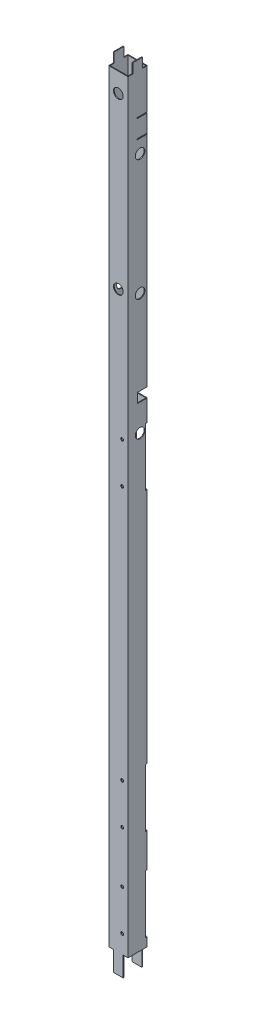
SolidWorks part; units mm, degrees
ref_plane "Front Plane" through (0, 0, 0) normal (0, 0, 1) x (1, 0, 0)
ref_plane "Top Plane" through (0, 0, 0) normal (0, 1, 0) x (1, 0, 0)
ref_plane "Right Plane" through (0, 0, 0) normal (1, 0, 0) x (0, 0, -1)
sketch "Sketch1" plane through (0, 0, 0) normal (0, 1, 0) x (1, 0, 0)
  line L0 (1.5, 1.5) -> (38.5, 1.5)
  line L1 (0.5, 0) -> (39.5, 0)
  line L2 (0, 0.5) -> (0, 39.5)
  line L3 (0.5, 40) -> (39.5, 40)
  line L4 (40, 0.5) -> (40, 39.5)
  line L5 (38.5, 1.5) -> (38.5, 38.5)
  line L6 (1.5, 38.5) -> (38.5, 38.5)
  line L7 (1.5, 1.5) -> (1.5, 38.5)
  arc A0 (39.5, 0) -> (40, 0.5) centre (39.5, 0.5) ccw
  arc A1 (0.5, 0) -> (0, 0.5) centre (0.5, 0.5) cw
  arc A2 (0, 39.5) -> (0.5, 40) centre (0.5, 39.5) cw
  arc A3 (39.5, 40) -> (40, 39.5) centre (39.5, 39.5) cw
  arc A4 (38.5, 1.5) -> (38.5, 1.5) centre (38.5, 1.5) ccw
  arc A5 (38.5, 38.5) -> (38.5, 38.5) centre (38.5, 38.5) cw
  arc A6 (1.5, 38.5) -> (1.5, 38.5) centre (1.5, 38.5) cw
  arc A7 (1.5, 1.5) -> (1.5, 1.5) centre (1.5, 1.5) cw
  point P9 (0, 0)
  dimension "D3" = 0.5
  dimension "D1" = 40
  dimension "D2" = 40
  dimension "D4" = 1.5
extrude "Boss-Extrude1" add sketch "Sketch1" along normal blind 1637.5
sketch "Sketch2" plane through (40, 0, 0) normal (1, 0, 0) x (0, 0, -1)
  line L0 (20, 1637.5) -> (20, 1563.8814) construction
  line L1 (40, 1637.5) -> (30, 1637.5)
  line L2 (40, 1637.5) -> (40, 1617.5)
  line L3 (40, 1617.5) -> (30, 1617.5)
  line L4 (30, 1637.5) -> (30, 1617.5)
  line L5 (0.5, 1637.5) -> (39.5, 1637.5) construction
  line L6 (10, 1637.5) -> (10, 1617.5)
  line L7 (0, 1617.5) -> (10, 1617.5)
  line L8 (0, 1637.5) -> (0, 1617.5)
  line L9 (0, 1637.5) -> (10, 1637.5)
  dimension "D1" = 20
  dimension "D2" = 10
extrude "Cut-Extrude1" cut sketch "Sketch2" against normal blind 40
sketch "Sketch3" plane through (40, 0, 0) normal (1, 0, 0) x (0, 0, -1)
  line L0 (40, 1617.5) -> (40, 0) construction
  line L1 (40, 1535) -> (19, 1535)
  line L2 (40, 1535) -> (40, 1533)
  line L3 (40, 1533) -> (19, 1533)
  line L4 (19, 1535) -> (19, 1533)
  line L5 (30, 1617.5) -> (39.5, 1617.5) construction
  line L6 (40, 1515) -> (25.1946, 1515) construction
  line L7 (40, 1617.5) -> (40, 0) construction
  line L8 (19, 1495) -> (19, 1497)
  line L9 (40, 1497) -> (19, 1497)
  line L10 (40, 1495) -> (40, 1497)
  line L11 (40, 1495) -> (19, 1495)
  point P9 (34.75, 1617.5)
  dimension "D1" = 2
  dimension "D2" = 82.5
  dimension "D3" = 21
  dimension "D4" = 20
extrude "Cut-Extrude2" cut sketch "Sketch3" against normal blind 20
sketch "Sketch4" plane through (0, 0, 0) normal (0, 0, 1) x (1, 0, 0)
  line L0 (20, 0) -> (20, 31.6489) construction
  line L1 (40, 0) -> (30, 0)
  line L2 (40, 0) -> (40, 41)
  line L3 (40, 41) -> (30, 41)
  line L4 (30, 0) -> (30, 41)
  line L5 (0.5, 0) -> (39.5, 0) construction
  line L6 (10, 0) -> (10, 41)
  line L7 (0, 41) -> (10, 41)
  line L8 (0, 0) -> (0, 41)
  line L9 (0, 0) -> (10, 0)
  dimension "D1" = 10
  dimension "D2" = 41
extrude "Cut-Extrude3" cut sketch "Sketch4" against normal through all
sketch "Sketch5" plane through (40, 0, -40) normal (0, 0, 1) x (1, 0, 0)
  line L0 (-40, 190.5) -> (-20, 190.5)
  line L2 (-20, 190.5) -> (-20, 231)
  line L3 (-20, 231) -> (-30, 231)
  line L4 (-30, 231) -> (-30, 211)
  line L5 (-30, 211) -> (-40, 211)
  line L8 (-40, 190.5) -> (-40, 211)
  line L10 (-40, 380.5) -> (-20, 380.5)
  line L11 (-20, 380.5) -> (-20, 421)
  line L12 (-20, 421) -> (-30, 421)
  line L13 (-30, 421) -> (-30, 401)
  line L14 (-30, 401) -> (-40, 401)
  line L15 (-40, 380.5) -> (-40, 401)
  line L16 (-40, 570.5) -> (-20, 570.5)
  line L17 (-20, 570.5) -> (-20, 611)
  line L18 (-20, 611) -> (-30, 611)
  line L19 (-30, 611) -> (-30, 591)
  line L20 (-30, 591) -> (-40, 591)
  line L21 (-40, 570.5) -> (-40, 591)
  line L22 (-40, 760.5) -> (-20, 760.5)
  line L23 (-20, 760.5) -> (-20, 801)
  line L24 (-20, 801) -> (-30, 801)
  line L25 (-30, 801) -> (-30, 781)
  line L26 (-30, 781) -> (-40, 781)
  line L27 (-40, 760.5) -> (-40, 781)
  line L28 (-40, 1617.5) -> (-40, 41) construction
  dimension "D1" = 20
  dimension "D2" = 10
  dimension "D3" = 20.5
  dimension "D4" = 20
  dimension "D6" = 4
extrude "Cut-Extrude4" cut sketch "Sketch5" along normal blind 20
sketch "Sketch7" plane through (40, 0, 0) normal (1, 0, 0) x (0, 0, -1)
  line L0 (40, 1495) -> (40, 41) construction
  line L1 (20, 1023) -> (40, 1023)
  line L2 (20, 1023) -> (20, 1043)
  line L3 (20, 1043) -> (40, 1043)
  line L4 (40, 1023) -> (40, 1043)
  line L5 (39.5, 41) -> (0.5, 41) construction
  dimension "D1" = 20
  dimension "D2" = 20
  dimension "D3" = 982
extrude "Cut-Extrude6" cut sketch "Sketch7" against normal blind 20
sketch "Sketch8" plane through (40, 0, 0) normal (1, 0, 0) x (0, 0, -1)
  line L1 (36, 59) -> (40, 59)
  line L2 (36, 59) -> (36, 179)
  line L3 (36, 179) -> (40, 179)
  line L4 (40, 59) -> (40, 179)
  line L5 (40, 1023) -> (40, 41) construction
  line L6 (39.5, 41) -> (0.5, 41) construction
  dimension "D1" = 18
  dimension "D2" = 120
  dimension "D3" = 4
extrude "Cut-Extrude7" cut sketch "Sketch8" against normal blind 22
sketch "Sketch9" plane through (0, 0, -1.5) normal (0, 0, -1) x (-1, 0, 0)
  line L0 (-18, 59) -> (-39.5, 59) construction
  line L1 (-38.5, 1617.5) -> (-38.5, 41) construction
  circle A0 centre (-28, 162.5) radius 3
  circle A1 centre (-28, 78.5) radius 3
  dimension "D1" = 6
  dimension "D2" = 84
  dimension "D3" = 19.5
  dimension "D4" = 10.5
extrude "Cut-Extrude8" cut sketch "Sketch9" against normal blind 22
pattern_linear "LPattern1" count 2 spacing 190 along (0, 1, 0) of "Cut-Extrude7", "Cut-Extrude8"
pattern_linear "LPattern2" count 2 spacing 800 along (0, 1, 0) of "Cut-Extrude7", "Cut-Extrude8"
sketch "Sketch10" plane through (0, 0, 0) normal (0, 0, 1) x (1, 0, 0)
  line L0 (0.5, 1617.5) -> (39.5, 1617.5) construction
  line L1 (0, 1617.5) -> (0, 41) construction
  circle A0 centre (20, 1577.5) radius 10
  circle A1 centre (20, 1227.5) radius 10
  dimension "D1" = 20
  dimension "D2" = 40
  dimension "D3" = 20
  dimension "D4" = 350
extrude "Cut-Extrude9" cut sketch "Sketch10" against normal through all
sketch "Sketch11" plane through (0, 0, 0) normal (-1, 0, 0) x (0, 0, 1)
  line L0 (-30, 1617.5) -> (-39.5, 1617.5) construction
  line L1 (-40, 1617.5) -> (-40, 781) construction
  circle A0 centre (-25, 1467.5) radius 10
  circle A1 centre (-25, 1217.5) radius 10
  circle A2 centre (-25, 967.5) radius 10
  dimension "D1" = 150
  dimension "D2" = 20
  dimension "D3" = 15
  dimension "D4" = 3
extrude "Cut-Extrude10" cut sketch "Sketch11" against normal through all
